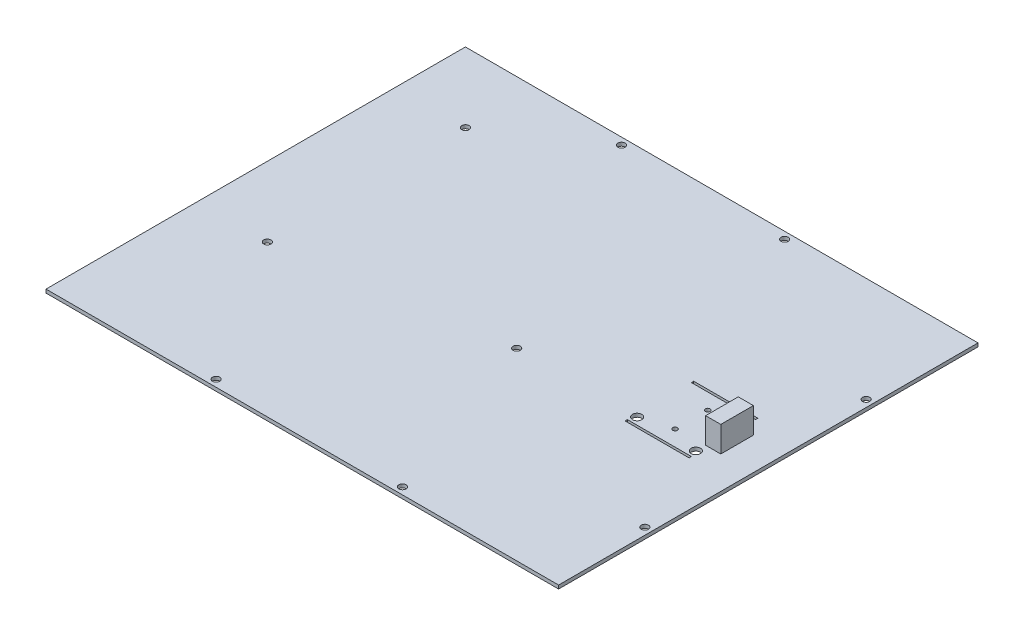
SolidWorks part; units mm, degrees
ref_plane "Front Plane" through (0, 0, 0) normal (0, 0, 1) x (1, 0, 0)
ref_plane "Top Plane" through (0, 0, 0) normal (0, 1, 0) x (1, 0, 0)
ref_plane "Right Plane" through (0, 0, 0) normal (1, 0, 0) x (0, 0, -1)
sketch "Sketch1" plane through (0, 0, 0) normal (0, 1, 0) x (1, 0, 0)
  line L0 (0, 0) -> (220, 0)
  line L1 (0, 0) -> (0, 180)
  line L2 (220, 0) -> (220, 180)
  line L3 (0, 180) -> (220, 180)
  line L4 (0, 90) -> (220, 90) construction
  line L5 (110, 180) -> (110, 0) construction
  line L6 (30, 177) -> (217, 177) construction
  line L7 (30, 177) -> (30, 3) construction
  line L8 (217, 177) -> (217, 3) construction
  line L9 (30, 3) -> (217, 3) construction
  line L10 (30, 150) -> (217, 150) construction
  line L11 (217, 65) -> (30, 65) construction
  circle A0 centre (70, 177) radius 1.55
  circle A1 centre (140, 177) radius 1.55
  circle A2 centre (30, 150) radius 1.55
  circle A3 centre (30, 65) radius 1.55
  circle A4 centre (217, 40) radius 1.55
  circle A5 centre (217, 135) radius 1.55
  circle A6 centre (70, 3) radius 1.55
  circle A7 centre (150, 3) radius 1.55
  circle A8 centre (123, 79) radius 1.55
  dimension "D7" = 3.1
  dimension "D8" = 3.1
  dimension "D9" = 3.1
  dimension "D10" = 3.1
  dimension "D11" = 3.1
  dimension "D12" = 3.1
  dimension "D13" = 3.1
  dimension "D14" = 3.1
  dimension "D15" = 30
  dimension "D20" = 40
  dimension "D18" = 70
  dimension "D21" = 70
  dimension "D22" = 80
  dimension "D23" = 3.1
  dimension "D24" = 123
  dimension "D25" = 79
  dimension "D1" = 180
  dimension "D2" = 220
  dimension "D3" = 3
  dimension "D4" = 30
  dimension "D5" = 3
  dimension "D6" = 3
  dimension "D16" = 65
  dimension "D17" = 70
  dimension "D19" = 45
extrude "Boss-Extrude1" add sketch "Sketch1" along normal blind 1.5
ref_plane "Z" through (0, 0, -90) normal (0, 0, 1) x (1, 0, 0)
ref_plane "X" through (110, 0, 0) normal (-1, 0, 0) x (0, 0, 1)
sketch "Эскиз1" plane through (0, 1.5, 0) normal (0, 1, 0) x (1, 0, 0)
  line L0 (202.75, 103.75) -> (202.75, 76.25) construction
  line L1 (202.75, 103.75) -> (202.75, 76.25) construction
  line L2 (200.75, 74.25) -> (173.25, 74.25) construction
  line L3 (200.75, 74.25) -> (173.25, 74.25) construction
  line L4 (203.75, 75.25) -> (203.75, 104.75)
  line L5 (201.75, 106.75) -> (172.25, 106.75)
  line L6 (170.25, 104.75) -> (170.25, 75.25)
  line L7 (172.25, 73.25) -> (201.75, 73.25)
  line L8 (203.75, 75.25) -> (203.75, 104.75) construction
  line L9 (201.75, 106.75) -> (172.25, 106.75) construction
  line L10 (170.25, 104.75) -> (170.25, 75.25) construction
  line L11 (172.25, 73.25) -> (201.75, 73.25) construction
  line L12 (173.25, 105.75) -> (200.75, 105.75) construction
  line L13 (173.25, 105.75) -> (200.75, 105.75) construction
  line L14 (171.25, 103.75) -> (171.25, 76.25) construction
  line L15 (187, 73.25) -> (187, 106.75) construction
  line L16 (173.25, 75.25) -> (173.25, 76.25)
  line L17 (173.25, 75.25) -> (200.75, 75.25)
  line L18 (173.25, 76.25) -> (200.75, 76.25)
  line L19 (200.75, 75.25) -> (200.75, 76.25)
  line L20 (170.25, 90) -> (203.75, 90) construction
  line L21 (200.75, 104.75) -> (200.75, 103.75)
  line L22 (173.25, 104.75) -> (200.75, 104.75)
  line L23 (173.25, 104.75) -> (173.25, 103.75)
  line L24 (173.25, 103.75) -> (200.75, 103.75)
  line L26 (187, 106.75) -> (187, 74.25) construction
  line L27 (0, 180) -> (0, 0) construction
  line L28 (220, 180) -> (0, 180) construction
  arc A0 (202.75, 103.75) -> (200.75, 105.75) centre (200.75, 103.75) ccw construction
  arc A1 (202.75, 103.75) -> (200.75, 105.75) centre (200.75, 103.75) ccw construction
  arc A2 (200.75, 74.25) -> (202.75, 76.25) centre (200.75, 76.25) ccw construction
  arc A3 (200.75, 74.25) -> (202.75, 76.25) centre (200.75, 76.25) ccw construction
  arc A4 (203.75, 104.75) -> (201.75, 106.75) centre (201.75, 104.75) ccw
  arc A5 (172.25, 106.75) -> (170.25, 104.75) centre (172.25, 104.75) ccw
  arc A6 (170.25, 75.25) -> (172.25, 73.25) centre (172.25, 75.25) ccw
  arc A7 (201.75, 73.25) -> (203.75, 75.25) centre (201.75, 75.25) ccw
  arc A8 (203.75, 104.75) -> (201.75, 106.75) centre (201.75, 104.75) ccw construction
  arc A9 (172.25, 106.75) -> (170.25, 104.75) centre (172.25, 104.75) ccw construction
  arc A10 (170.25, 75.25) -> (172.25, 73.25) centre (172.25, 75.25) ccw construction
  arc A11 (201.75, 73.25) -> (203.75, 75.25) centre (201.75, 75.25) ccw construction
  arc A12 (173.25, 74.25) -> (171.25, 76.25) centre (173.25, 76.25) cw construction
  arc A13 (171.25, 103.75) -> (173.25, 105.75) centre (173.25, 103.75) cw construction
  circle A14 centre (187, 83) radius 1
  circle A15 centre (187, 97) radius 1
  circle A17 centre (199.6, 79.3) radius 2
  circle A18 centre (199.6, 100.7) radius 2
  circle A19 centre (174.4, 79.3) radius 2
  dimension "D6" = 7
  dimension "D7" = 2
  dimension "D8" = 12.6
  dimension "D10" = 4
  dimension "D11" = 12.6
  dimension "D12" = 10.7
  dimension "D14" = 4
  dimension "D16" = 10.7
  dimension "D2" = 2
  dimension "D3" = 1
  dimension "D4" = 2
  dimension "D5" = 2
  dimension "D9" = 10.7
  dimension "D13" = 187
  dimension "D15" = 90
  dimension "D1" = 0
extrude "Вырез-Вытянуть1" cut sketch "Эскиз1" against normal through all
sketch "Sketch2" plane through (0, 1.5, 0) normal (0, 1, 0) x (1, 0, 0)
  line L0 (0, 138) -> (119.3, 138) construction
  line L1 (0, 138) -> (0, 72) construction
  line L2 (119.3, 138) -> (119.3, 72) construction
  line L3 (0, 72) -> (119.3, 72) construction
  line L4 (0, 180) -> (0, 0) construction
  line L5 (220, 180) -> (0, 180) construction
  line L6 (85.48, 131.67) -> (85.48, 72) construction
  circle A0 centre (85.48, 131.67) radius 1
  circle A1 centre (85.48, 80.87) radius 1
  dimension "D4" = 33.82
  dimension "D5" = 6.33
  dimension "D6" = 2
  dimension "D7" = 50.8
  dimension "D8" = 2
  dimension "D1" = 42
  dimension "D2" = 66
  dimension "D3" = 119.3
sketch "Sketch3" plane through (0, 1.5, 0) normal (0, 1, 0) x (1, 0, 0)
  line L0 (199.6, 83.5) -> (199.6, 97.5)
  line L1 (199.6, 83.5) -> (206.1, 83.5)
  line L2 (199.6, 97.5) -> (206.1, 97.5)
  line L3 (206.1, 83.5) -> (206.1, 97.5)
  line L4 (187, 76.25) -> (187, 104.75) construction
  line L5 (200.75, 76.25) -> (173.25, 76.25) construction
  line L6 (200.75, 104.75) -> (173.25, 104.75) construction
  line L7 (187, 90.5) -> (206.1, 90.5) construction
  line L8 (199.6, 90.5) -> (206.1, 90.5) construction
  line L9 (199.6, 79.3) -> (199.6, 100.7) construction
  dimension "D1" = 6.5
  dimension "D2" = 14
extrude "Boss-Extrude2" add sketch "Sketch3" along normal blind 11
